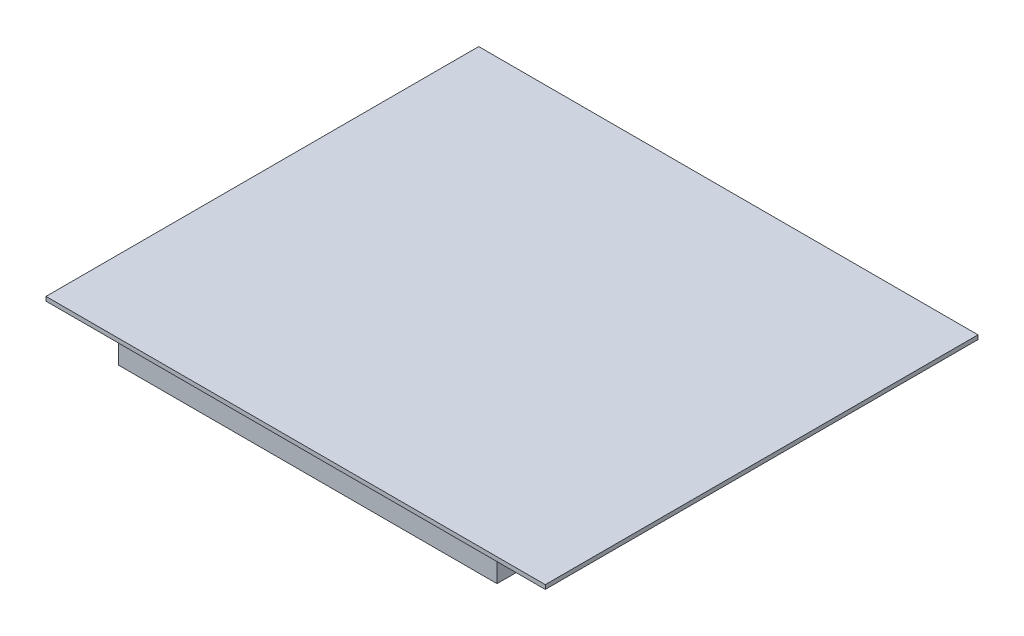
SolidWorks part; units mm, degrees
ref_plane "Спереди" through (0, 0, 0) normal (0, 0, 1) x (1, 0, 0)
ref_plane "Сверху" through (0, 0, 0) normal (0, 1, 0) x (1, 0, 0)
ref_plane "Справа" through (0, 0, 0) normal (1, 0, 0) x (0, 0, -1)
sketch "Эскиз1" plane through (0, 0, 0) normal (0, 1, 0) x (1, 0, 0)
  line L1 (300, -260) -> (-300, -260)
  line L2 (300, -260) -> (300, 260)
  line L3 (300, 260) -> (-300, 260)
  line L4 (-300, -260) -> (-300, 260)
  line L5 (300, -260) -> (-300, 260) construction
  line L6 (300, 260) -> (-300, -260) construction
  point P0 (0, 0)
  dimension "D1" = 600
  dimension "D2" = 520
extrude "Бобышка-Вытянуть1" add sketch "Эскиз1" along normal blind 5
sketch "Эскиз3" plane through (0, 0, 0) normal (0, -1, 0) x (1, 0, 0)
  line L0 (-300, 260) -> (300, 260) construction
  line L1 (220, -248) -> (-235, -248)
  line L2 (220, -248) -> (220, 238)
  line L3 (220, 238) -> (-235, 238)
  line L4 (-235, -248) -> (-235, 238)
  line L5 (220, -248) -> (-235, 238) construction
  line L6 (220, 238) -> (-235, -248) construction
  line L8 (300, 260) -> (300, -260) construction
  point P0 (-7.5, -5)
  dimension "D1" = 22
  dimension "D2" = 486
  dimension "D3" = 80
  dimension "D4" = 455
extrude "Бобышка-Вытянуть2" add sketch "Эскиз3" along normal blind 45
